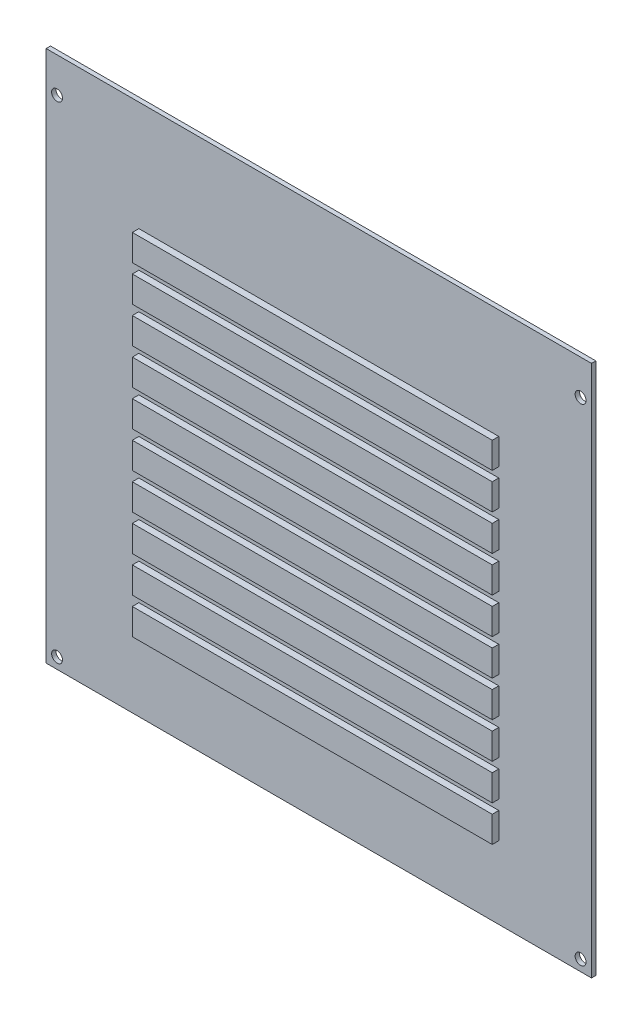
SolidWorks part; units mm, degrees
ref_plane "Ebene vorne" through (0, 0, 0) normal (0, 0, 1) x (1, 0, 0)
ref_plane "Ebene oben" through (0, 0, 0) normal (0, 1, 0) x (1, 0, 0)
ref_plane "Ebene rechts" through (0, 0, 0) normal (1, 0, 0) x (0, 0, -1)
sketch "Skizze1" plane through (0, 0, 0) normal (0, 0, 1) x (1, 0, 0)
  line L1 (0, 0) -> (-250, 0)
  line L2 (0, 0) -> (0, 244)
  line L3 (0, 244) -> (-250, 244)
  line L4 (-250, 0) -> (-250, 244)
  dimension "D1" = 250
  dimension "D2" = 244
extrude "Aufsatz-Linear austragen1" add sketch "Skizze1" along normal blind 2
sketch "Skizze2" plane through (0, 0, 2) normal (0, 0, 1) x (1, 0, 0)
  line L0 (-250, 0) -> (0, 0) construction
  line L1 (-250, 244) -> (-250, 0) construction
  line L2 (0, 0) -> (0, 244) construction
  circle A0 centre (-245, 5) radius 2.5
  circle A1 centre (-5, 5) radius 2.5
  circle A2 centre (-245, 228) radius 2.5
  circle A4 centre (-5, 228) radius 2.5
  dimension "D1" = 5
  dimension "D2" = 5
  dimension "D3" = 5
  dimension "D4" = 5
  dimension "D5" = 223
extrude "Schnitt-Linear austragen1" cut sketch "Skizze2" against normal blind 2
sketch "Skizze3" plane through (0, 0, 2) normal (0, 0, 1) x (1, 0, 0)
  line L0 (-250, 0) -> (0, 0) construction
  line L1 (-207.5, 45.25) -> (-42.5, 45.25)
  line L2 (-207.5, 45.25) -> (-207.5, 33.25)
  line L3 (-207.5, 33.25) -> (-42.5, 33.25)
  line L4 (-42.5, 45.25) -> (-42.5, 33.25)
  line L5 (0, 0) -> (0, 244) construction
  line L6 (-250, 244) -> (-250, 0) construction
  line L43 (-207.5, 61.75) -> (-207.5, 49.75)
  line L44 (-207.5, 47.5) -> (-42.5, 47.5) construction
  line L45 (-207.5, 47.5) -> (-207.5, 31) construction
  line L46 (-207.5, 31) -> (-42.5, 31) construction
  line L47 (-42.5, 47.5) -> (-42.5, 31) construction
  line L48 (-207.5, 61.75) -> (-42.5, 61.75)
  line L49 (-42.5, 61.75) -> (-42.5, 49.75)
  line L50 (-207.5, 49.75) -> (-42.5, 49.75)
  line L51 (-207.5, 64) -> (-42.5, 64) construction
  line L52 (-42.5, 64) -> (-42.5, 47.5) construction
  line L53 (-207.5, 47.5) -> (-42.5, 47.5) construction
  line L54 (-207.5, 64) -> (-207.5, 47.5) construction
  line L55 (-207.5, 78.25) -> (-207.5, 66.25)
  line L56 (-207.5, 78.25) -> (-42.5, 78.25)
  line L57 (-42.5, 78.25) -> (-42.5, 66.25)
  line L58 (-207.5, 66.25) -> (-42.5, 66.25)
  line L59 (-207.5, 80.5) -> (-42.5, 80.5) construction
  line L60 (-42.5, 80.5) -> (-42.5, 64) construction
  line L61 (-207.5, 64) -> (-42.5, 64) construction
  line L62 (-207.5, 80.5) -> (-207.5, 64) construction
  line L63 (-207.5, 94.75) -> (-207.5, 82.75)
  line L64 (-207.5, 94.75) -> (-42.5, 94.75)
  line L65 (-42.5, 94.75) -> (-42.5, 82.75)
  line L66 (-207.5, 82.75) -> (-42.5, 82.75)
  line L67 (-207.5, 97) -> (-42.5, 97) construction
  line L68 (-42.5, 97) -> (-42.5, 80.5) construction
  line L69 (-207.5, 80.5) -> (-42.5, 80.5) construction
  line L70 (-207.5, 97) -> (-207.5, 80.5) construction
  line L71 (-207.5, 111.25) -> (-207.5, 99.25)
  line L72 (-207.5, 111.25) -> (-42.5, 111.25)
  line L73 (-42.5, 111.25) -> (-42.5, 99.25)
  line L74 (-207.5, 99.25) -> (-42.5, 99.25)
  line L75 (-207.5, 113.5) -> (-42.5, 113.5) construction
  line L76 (-42.5, 113.5) -> (-42.5, 97) construction
  line L77 (-207.5, 97) -> (-42.5, 97) construction
  line L78 (-207.5, 113.5) -> (-207.5, 97) construction
  line L79 (-207.5, 127.75) -> (-207.5, 115.75)
  line L80 (-207.5, 127.75) -> (-42.5, 127.75)
  line L81 (-42.5, 127.75) -> (-42.5, 115.75)
  line L82 (-207.5, 115.75) -> (-42.5, 115.75)
  line L83 (-207.5, 130) -> (-42.5, 130) construction
  line L84 (-42.5, 130) -> (-42.5, 113.5) construction
  line L85 (-207.5, 113.5) -> (-42.5, 113.5) construction
  line L86 (-207.5, 130) -> (-207.5, 113.5) construction
  line L87 (-207.5, 144.25) -> (-207.5, 132.25)
  line L88 (-207.5, 144.25) -> (-42.5, 144.25)
  line L89 (-42.5, 144.25) -> (-42.5, 132.25)
  line L90 (-207.5, 132.25) -> (-42.5, 132.25)
  line L91 (-207.5, 146.5) -> (-42.5, 146.5) construction
  line L92 (-42.5, 146.5) -> (-42.5, 130) construction
  line L93 (-207.5, 130) -> (-42.5, 130) construction
  line L94 (-207.5, 146.5) -> (-207.5, 130) construction
  line L95 (-207.5, 160.75) -> (-207.5, 148.75)
  line L96 (-207.5, 160.75) -> (-42.5, 160.75)
  line L97 (-42.5, 160.75) -> (-42.5, 148.75)
  line L98 (-207.5, 148.75) -> (-42.5, 148.75)
  line L99 (-207.5, 163) -> (-42.5, 163) construction
  line L100 (-42.5, 163) -> (-42.5, 146.5) construction
  line L101 (-207.5, 146.5) -> (-42.5, 146.5) construction
  line L102 (-207.5, 163) -> (-207.5, 146.5) construction
  line L103 (-207.5, 177.25) -> (-207.5, 165.25)
  line L104 (-207.5, 177.25) -> (-42.5, 177.25)
  line L105 (-42.5, 177.25) -> (-42.5, 165.25)
  line L106 (-207.5, 165.25) -> (-42.5, 165.25)
  line L107 (-207.5, 179.5) -> (-42.5, 179.5) construction
  line L108 (-42.5, 179.5) -> (-42.5, 163) construction
  line L109 (-207.5, 163) -> (-42.5, 163) construction
  line L110 (-207.5, 179.5) -> (-207.5, 163) construction
  line L111 (-207.5, 193.75) -> (-207.5, 181.75)
  line L112 (-207.5, 193.75) -> (-42.5, 193.75)
  line L113 (-42.5, 193.75) -> (-42.5, 181.75)
  line L114 (-207.5, 181.75) -> (-42.5, 181.75)
  line L115 (-207.5, 196) -> (-42.5, 196) construction
  line L116 (-42.5, 196) -> (-42.5, 179.5) construction
  line L117 (-207.5, 179.5) -> (-42.5, 179.5) construction
  line L118 (-207.5, 196) -> (-207.5, 179.5) construction
  point P14 (-207.5, 39.25)
  point P15 (-207.5, 39.25)
  dimension "D1" = 33.25
  dimension "D2" = 12
  dimension "D3" = 42.5
  dimension "D4" = 42.5
  dimension "D6" = 10
  dimension "D5" = 16.5
extrude "Aufsatz-Linear austragen2" add sketch "Skizze3" along normal blind 3
